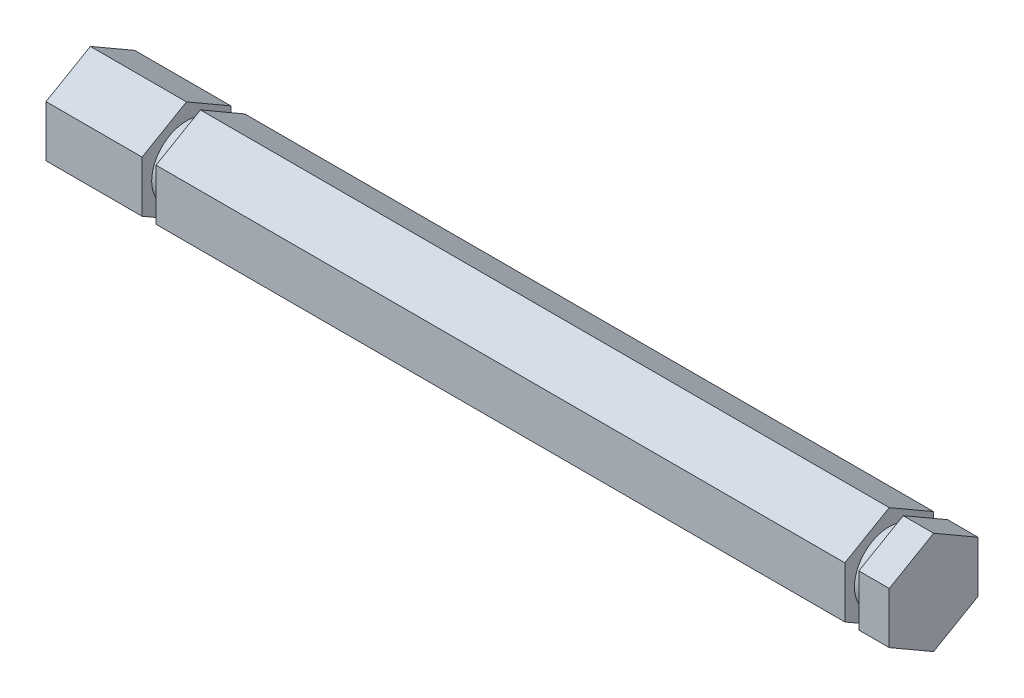
SolidWorks part; units mm, degrees
material "6061-T6 (SS)"
ref_plane "Front" through (0, 0, 0) normal (0, 0, 1) x (1, 0, 0)
ref_plane "Top" through (0, 0, 0) normal (0, 1, 0) x (1, 0, 0)
ref_plane "Right" through (0, 0, 0) normal (1, 0, 0) x (0, 0, -1)
sketch "Sketch1" plane through (0, 0, 0) normal (1, 0, 0) x (0, 0, -1)
  line L1 (0, 7.3323) -> (-6.35, 3.6662)
  line L2 (-6.35, 3.6662) -> (-6.35, -3.6662)
  line L3 (-6.35, -3.6662) -> (0, -7.3323)
  line L4 (0, -7.3323) -> (6.35, -3.6662)
  line L5 (6.35, -3.6662) -> (6.35, 3.6662)
  line L6 (6.35, 3.6662) -> (0, 7.3323)
  circle A0 centre (0, 0) radius 6.35 construction
  dimension "D1" = 12.7
extrude "Boss-Extrude1" add sketch "Sketch1" along normal blind 120.65
sketch "Sketch2" plane through (0, 0, 0) normal (0, 0, 1) x (1, 0, 0)
  line L0 (120.65, 7.3323) -> (0, 7.3323) construction
  line L1 (116.3, 7.3323) -> (114.3, 7.3323)
  line L2 (116.3, 7.3323) -> (116.3, 4.9784)
  line L3 (116.3, 4.9784) -> (114.3, 4.9784)
  line L4 (114.3, 7.3323) -> (114.3, 4.9784)
  line L5 (120.65, 7.3323) -> (120.65, 3.6662) construction
  line L6 (13.748, 7.3323) -> (15.748, 7.3323)
  line L7 (13.748, 7.3323) -> (13.748, 4.9784)
  line L8 (13.748, 4.9784) -> (15.748, 4.9784)
  line L9 (15.748, 7.3323) -> (15.748, 4.9784)
  line L10 (0, 0) -> (21.5392, 0) construction
  dimension "D1" = 6.35
  dimension "D2" = 2
  dimension "D3" = 98.552
  dimension "D4" = 9.9568
revolve "Cut-Revolve1" cut sketch "Sketch2" angle 360 about L10
